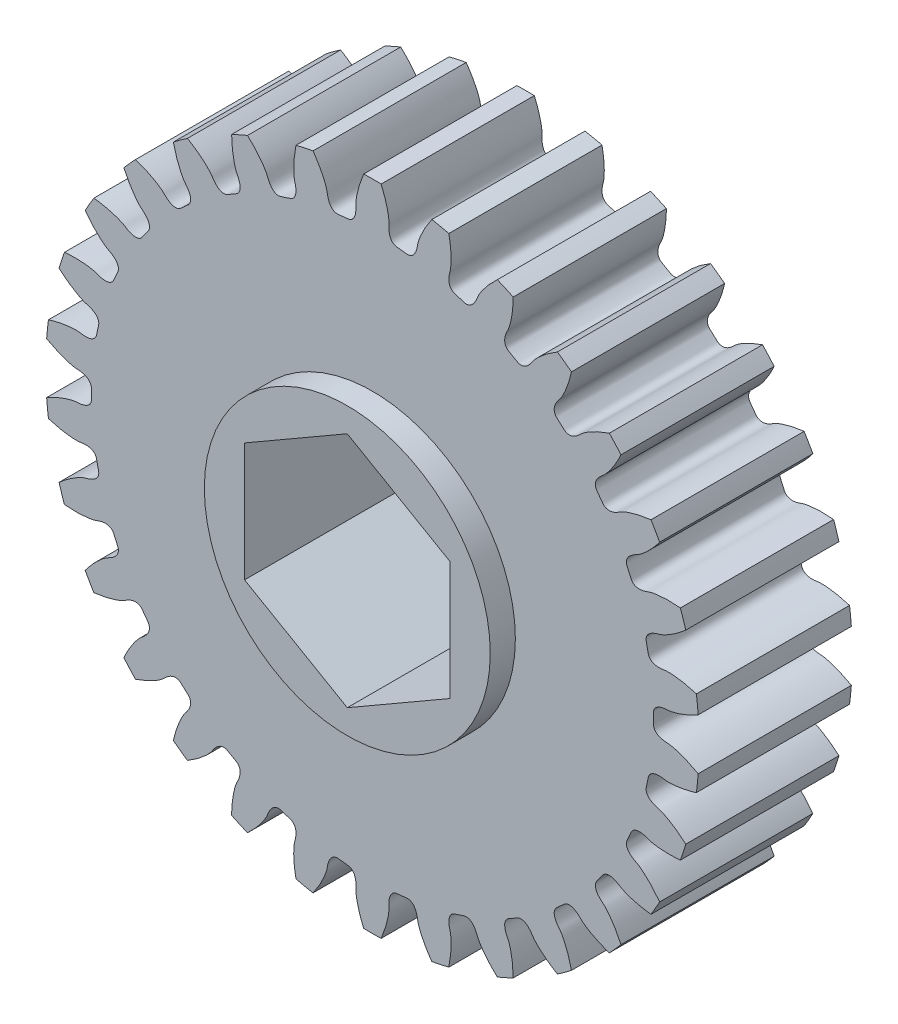
SolidWorks part; units mm, degrees
ref_plane "Front Plane" through (0, 0, 0) normal (0, 0, 1) x (1, 0, 0)
ref_plane "Top Plane" through (0, 0, 0) normal (0, 1, 0) x (1, 0, 0)
ref_plane "Right Plane" through (0, 0, 0) normal (1, 0, 0) x (0, 0, -1)
ref_plane "Plane1" through (0, 0, 4.7625) normal (0, 0, 1) x (1, 0, 0)
sketch "Sketch1" plane through (0, 0, 4.7625) normal (0, 0, 1) x (1, 0, 0)
  arc A0 (20.258, 1.5856) -> (20.145, 2.661) centre (0, 0) ccw
  arc A1 (19.4857, 5.7628) -> (19.1516, 6.7912) centre (0, 0) ccw
  arc A2 (17.8617, 9.6882) -> (17.3211, 10.6246) centre (0, 0) ccw
  arc A3 (15.4571, 13.1901) -> (14.7336, 13.9937) centre (0, 0) ccw
  arc A4 (12.377, 16.1156) -> (11.5022, 16.7512) centre (0, 0) ccw
  arc A5 (8.7559, 18.3368) -> (7.768, 18.7766) centre (0, 0) ccw
  arc A6 (4.7521, 19.7565) -> (3.6944, 19.9813) centre (0, 0) ccw
  arc A7 (0.5407, 20.3128) -> (-0.5407, 20.3128) centre (0, 0) ccw
  arc A8 (-3.6944, 19.9813) -> (-4.7521, 19.7565) centre (0, 0) ccw
  arc A9 (-7.768, 18.7766) -> (-8.7559, 18.3368) centre (0, 0) ccw
  arc A10 (-11.5022, 16.7512) -> (-12.377, 16.1156) centre (0, 0) ccw
  arc A11 (-14.7336, 13.9937) -> (-15.4571, 13.1901) centre (0, 0) ccw
  arc A12 (-17.3211, 10.6246) -> (-17.8617, 9.6882) centre (0, 0) ccw
  arc A13 (-19.1516, 6.7912) -> (-19.4857, 5.7628) centre (0, 0) ccw
  arc A14 (-20.145, 2.661) -> (-20.258, 1.5856) centre (0, 0) ccw
  arc A15 (-20.258, -1.5856) -> (-20.145, -2.661) centre (0, 0) ccw
  arc A16 (-19.4857, -5.7628) -> (-19.1516, -6.7912) centre (0, 0) ccw
  arc A17 (-17.8617, -9.6882) -> (-17.3211, -10.6246) centre (0, 0) ccw
  arc A18 (-15.4571, -13.1901) -> (-14.7336, -13.9937) centre (0, 0) ccw
  arc A19 (-12.377, -16.1156) -> (-11.5022, -16.7512) centre (0, 0) ccw
  arc A20 (-8.7559, -18.3368) -> (-7.768, -18.7766) centre (0, 0) ccw
  arc A21 (-4.7521, -19.7565) -> (-3.6944, -19.9813) centre (0, 0) ccw
  arc A22 (-0.5407, -20.3128) -> (0.5407, -20.3128) centre (0, 0) ccw
  arc A23 (3.6944, -19.9813) -> (4.7521, -19.7565) centre (0, 0) ccw
  arc A24 (7.768, -18.7766) -> (8.7559, -18.3368) centre (0, 0) ccw
  arc A25 (11.5022, -16.7512) -> (12.377, -16.1156) centre (0, 0) ccw
  arc A26 (14.7336, -13.9937) -> (15.4571, -13.1901) centre (0, 0) ccw
  arc A27 (17.3211, -10.6246) -> (17.8617, -9.6882) centre (0, 0) ccw
  arc A28 (19.1516, -6.7912) -> (19.4857, -5.7628) centre (0, 0) ccw
  arc A29 (20.145, -2.661) -> (20.258, -1.5856) centre (0, 0) ccw
  spline S0 degree 3 number of poles 93 (20.258, 1.5856) -> (20.258, -1.5856)
  spline S1 degree 3 number of poles 93 (19.4857, 5.7628) -> (20.145, 2.661)
  spline S2 degree 3 number of poles 93 (17.8617, 9.6882) -> (19.1516, 6.7912)
  spline S3 degree 3 number of poles 93 (15.4571, 13.1901) -> (17.3211, 10.6246)
  spline S4 degree 3 number of poles 93 (12.377, 16.1156) -> (14.7336, 13.9937)
  spline S5 degree 3 number of poles 93 (8.7559, 18.3368) -> (11.5022, 16.7512)
  spline S6 degree 3 number of poles 93 (4.7521, 19.7565) -> (7.768, 18.7766)
  spline S7 degree 3 number of poles 93 (0.5407, 20.3128) -> (3.6944, 19.9813)
  spline S8 degree 3 number of poles 93 (-3.6944, 19.9813) -> (-0.5407, 20.3128)
  spline S9 degree 3 number of poles 93 (-7.768, 18.7766) -> (-4.7521, 19.7565)
  spline S10 degree 3 number of poles 93 (-11.5022, 16.7512) -> (-8.7559, 18.3368)
  spline S11 degree 3 number of poles 93 (-14.7336, 13.9937) -> (-12.377, 16.1156)
  spline S12 degree 3 number of poles 93 (-17.3211, 10.6246) -> (-15.4571, 13.1901)
  spline S13 degree 3 number of poles 93 (-19.1516, 6.7912) -> (-17.8617, 9.6882)
  spline S14 degree 3 number of poles 93 (-20.145, 2.661) -> (-19.4857, 5.7628)
  spline S15 degree 3 number of poles 93 (-20.258, -1.5856) -> (-20.258, 1.5856)
  spline S16 degree 3 number of poles 93 (-19.4857, -5.7628) -> (-20.145, -2.661)
  spline S17 degree 3 number of poles 93 (-17.8617, -9.6882) -> (-19.1516, -6.7912)
  spline S18 degree 3 number of poles 93 (-15.4571, -13.1901) -> (-17.3211, -10.6246)
  spline S19 degree 3 number of poles 93 (-12.377, -16.1156) -> (-14.7336, -13.9937)
  spline S20 degree 3 number of poles 93 (-8.7559, -18.3368) -> (-11.5022, -16.7512)
  spline S21 degree 3 number of poles 93 (-4.7521, -19.7565) -> (-7.768, -18.7766)
  spline S22 degree 3 number of poles 93 (-0.5407, -20.3128) -> (-3.6944, -19.9813)
  spline S23 degree 3 number of poles 93 (3.6944, -19.9813) -> (0.5407, -20.3128)
  spline S24 degree 3 number of poles 93 (7.768, -18.7766) -> (4.7521, -19.7565)
  spline S25 degree 3 number of poles 93 (11.5022, -16.7512) -> (8.7559, -18.3368)
  spline S26 degree 3 number of poles 93 (14.7336, -13.9937) -> (12.377, -16.1156)
  spline S27 degree 3 number of poles 93 (17.3211, -10.6246) -> (15.4571, -13.1901)
  spline S28 degree 3 number of poles 93 (19.1516, -6.7912) -> (17.8617, -9.6882)
  spline S29 degree 3 number of poles 93 (20.145, -2.661) -> (19.4857, -5.7628)
extrude "Boss-Extrude1" add sketch "Sketch1" against normal blind 9.525
sketch "Sketch2" plane through (0, 0, 4.7625) normal (0, 0, 1) x (1, 0, 0)
  circle A0 centre (0, 0) radius 8.89
extrude "Boss-Extrude2" add sketch "Sketch2" along normal blind 1.5621
sketch "Sketch3" plane through (0, 0, -4.7625) normal (0, 0, -1) x (-1, 0, 0)
  circle A0 centre (0, 0) radius 8.89
extrude "Boss-Extrude3" add sketch "Sketch3" along normal blind 1.5621
sketch "Sketch4" plane through (0, 0, -6.3246) normal (0, 0, -1) x (-1, 0, 0)
  line L0 (6.3881, 3.6882) -> (0, 7.3763)
  line L1 (0, 7.3763) -> (-6.3881, 3.6882)
  line L2 (-6.3881, 3.6882) -> (-6.3881, -3.6882)
  line L3 (-6.3881, -3.6882) -> (0, -7.3763)
  line L4 (0, -7.3763) -> (6.3881, -3.6882)
  line L5 (6.3881, -3.6882) -> (6.3881, 3.6882)
extrude "Cut-Extrude1" cut sketch "Sketch4" against normal through all
